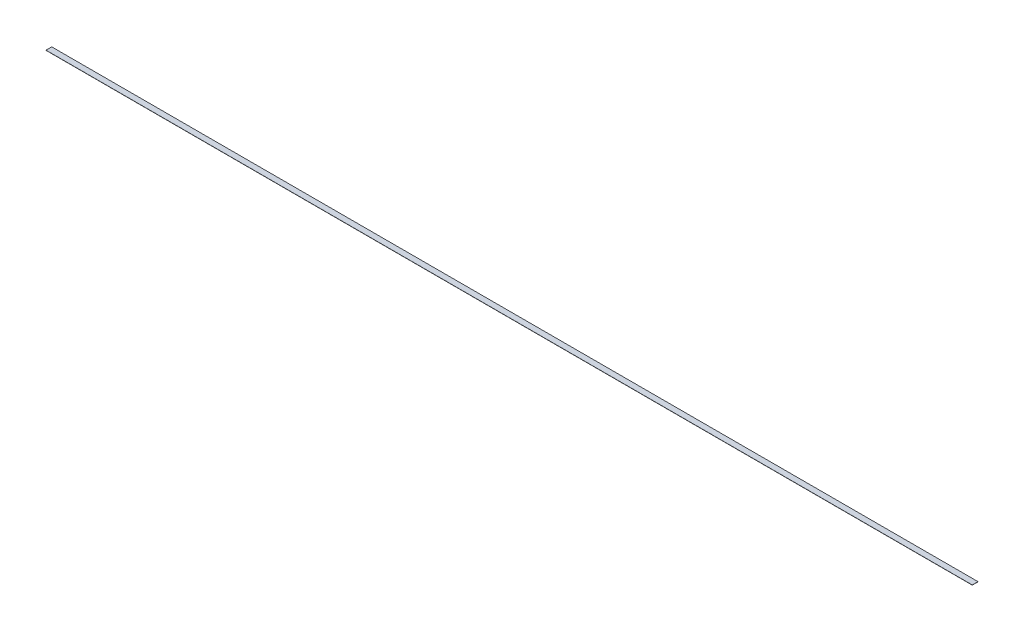
SolidWorks part; units mm, degrees
ref_plane "Front Plane" through (0, 0, 0) normal (0, 0, 1) x (1, 0, 0)
ref_plane "Top Plane" through (0, 0, 0) normal (0, 1, 0) x (1, 0, 0)
ref_plane "Right Plane" through (0, 0, 0) normal (1, 0, 0) x (0, 0, -1)
sketch "Sketch1" plane through (0, 0, 0) normal (0, 1, 0) x (1, 0, 0)
  line L1 (0, 0) -> (8204.2, 0)
  line L2 (0, 0) -> (0, 50.8)
  line L3 (0, 50.8) -> (8204.2, 50.8)
  line L4 (8204.2, 0) -> (8204.2, 50.8)
  dimension "D1" = 50.8
  dimension "D2" = 8204.2
extrude "Boss-Extrude1" add sketch "Sketch1" along normal blind 1.5875
